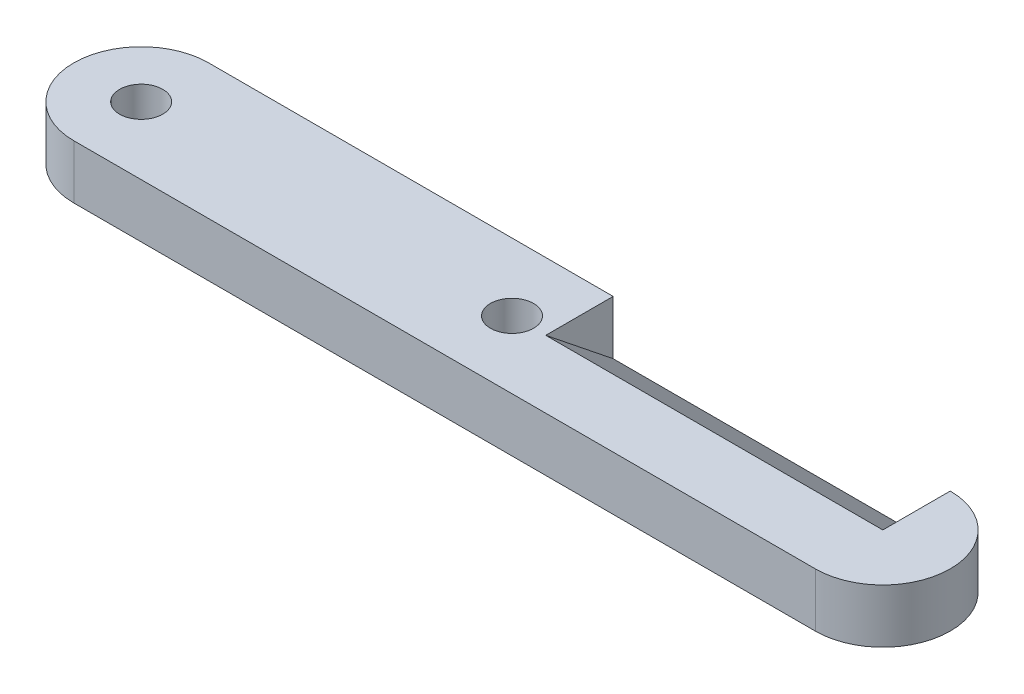
SolidWorks part; units mm, degrees
ref_plane "Front Plane" through (0, 0, 0) normal (0, 0, 1) x (1, 0, 0)
ref_plane "Top Plane" through (0, 0, 0) normal (0, 1, 0) x (1, 0, 0)
ref_plane "Right Plane" through (0, 0, 0) normal (1, 0, 0) x (0, 0, -1)
sketch "Sketch1" plane through (0, 0, 0) normal (0, 1, 0) x (1, 0, 0)
  line L0 (0, 0) -> (55, 0) construction
  line L1 (0, 5) -> (55, 5)
  line L2 (0, -5) -> (55, -5)
  arc A0 (0, 5) -> (0, -5) centre (0, 0) ccw
  arc A1 (55, -5) -> (55, 5) centre (55, 0) ccw
  point P3 (27.5, 0)
  dimension "D1" = 55
  dimension "D2" = 10
extrude "Boss-Extrude1" add sketch "Sketch1" along normal blind 4
sketch "Sketch2" plane through (0, 4, 0) normal (0, 1, 0) x (1, 0, 0)
  circle A0 centre (0, 0) radius 1.6
  circle A1 centre (27.5, 0) radius 1.6
  dimension "D1" = 3.2
  dimension "D2" = 3.2
  dimension "D3" = 27.5
extrude "Cut-Extrude1" cut sketch "Sketch2" against normal through all
sketch "Sketch3" plane through (0, 0, -5) normal (0, 0, -1) x (-1, 0, 0)
  line L0 (-55, 0) -> (0, 0) construction
  line L1 (-55, 4) -> (-30, 4)
  line L2 (-55, 4) -> (-55, 0)
  line L3 (-55, 0) -> (-30, 0)
  line L4 (-30, 4) -> (-30, 0)
  dimension "D1" = 25
extrude "Cut-Extrude2" cut sketch "Sketch3" against normal blind 5
sketch "Sketch4" plane through (55, 0, 0) normal (-1, 0, 0) x (0, 0, 1)
  line L0 (0, 4) -> (-5, 0)
  line L1 (5, 4) -> (-5, 4) construction
  line L2 (-5, 0) -> (5, 0) construction
  line L3 (-5, 0) -> (0, 0)
  line L4 (0, 0) -> (0, 4)
extrude "Boss-Extrude2" add sketch "Sketch4" along normal up to surface (25 mm away) up to face at (30, 2, -2.5)
